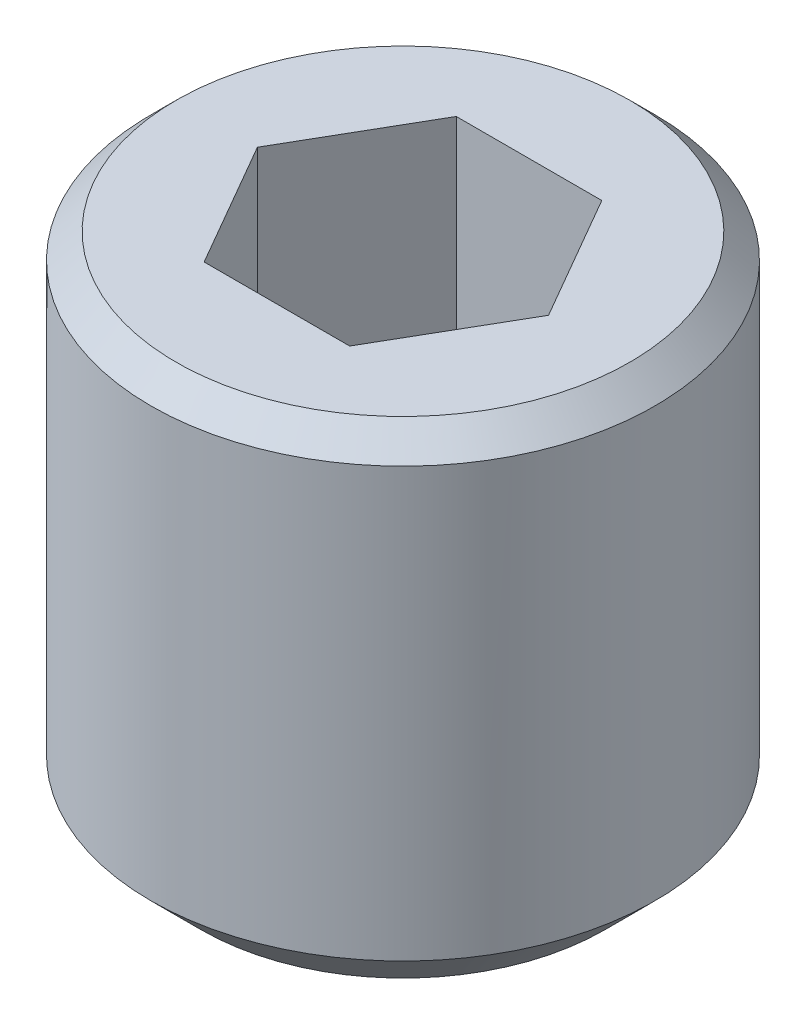
SolidWorks part; units mm, degrees
material "acero"
ref_plane "Alzado" through (0, 0, 0) normal (0, 0, 1) x (1, 0, 0)
ref_plane "Planta" through (0, 0, 0) normal (0, 1, 0) x (1, 0, 0)
ref_plane "Vista lateral" through (0, 0, 0) normal (1, 0, 0) x (0, 0, -1)
sketch "Croquis1" plane through (0, 0, 0) normal (0, 0, 1) x (1, 0, 0)
  line L0 (0, 0) -> (0, -60.9498) construction
  line L1 (0, 0) -> (1.5, 0)
  line L4 (1.5, 0) -> (1.5, -3)
  line L5 (1.5, -3) -> (0, -3)
  line L6 (0, -3) -> (0, 0)
  dimension "D1" = 3
  dimension "D4" = 3
revolve "Revolución1" add sketch "Croquis1" angle 360 about L0
cosmetic thread "Rosca cosmética1" parameters "D2"=2.439
sketch "Croquis3" plane through (0, 0, 0) normal (0, 1, 0) x (1, 0, 0)
  line L1 (-0.433, 0.75) -> (-0.866, 0)
  line L2 (-0.866, 0) -> (-0.433, -0.75)
  line L3 (-0.433, -0.75) -> (0.433, -0.75)
  line L4 (0.433, -0.75) -> (0.866, 0)
  line L5 (0.866, 0) -> (0.433, 0.75)
  line L6 (0.433, 0.75) -> (-0.433, 0.75)
  circle A0 centre (0, 0) radius 0.75 construction
  dimension "D1" = 1.5
extrude "Cortar-Extruir2" cut sketch "Croquis3" against normal blind 1.5
chamfer "Chaflán3" distance 0.3 angle 45 1 edges at (0, -3, 1.5)
chamfer "Chaflán4" distance 0.15 angle 45 1 edges at (0, 0, 1.5)
